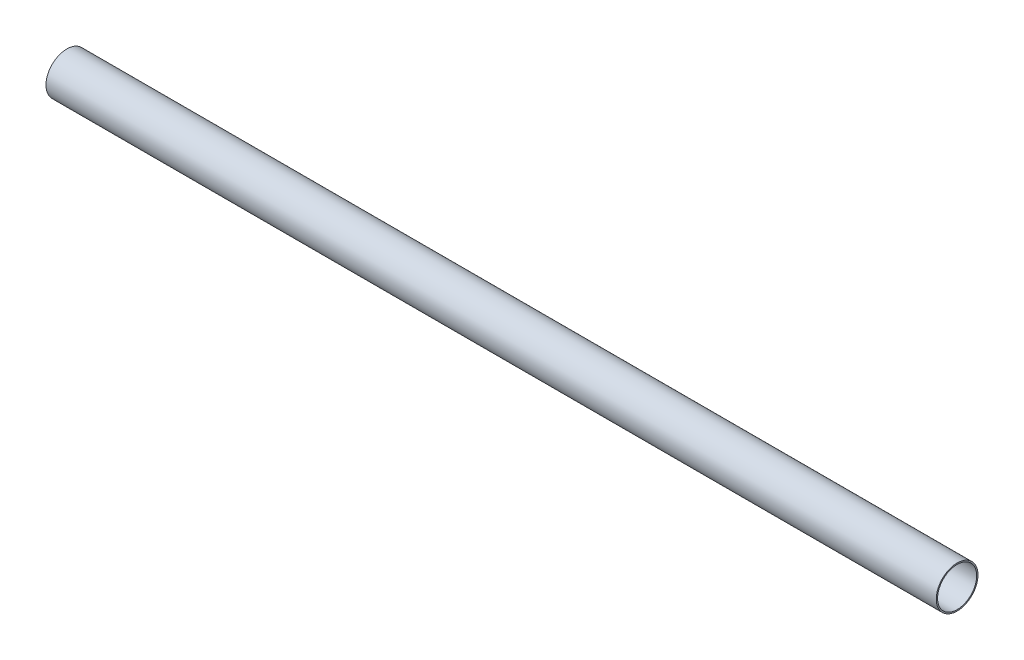
SolidWorks part; units mm, degrees
ref_plane "Front" through (0, 0, 0) normal (0, 0, 1) x (1, 0, 0)
ref_plane "Top" through (0, 0, 0) normal (0, 1, 0) x (1, 0, 0)
ref_plane "Right" through (0, 0, 0) normal (1, 0, 0) x (0, 0, -1)
sketch "Sketch1" plane through (0, 0, 0) normal (1, 0, 0) x (0, 0, -1)
  circle A0 centre (0, 0) radius 14.2875
  circle A1 centre (0, 0) radius 13.3985
  point P4 (14.2875, 0)
  point P5 (13.3985, 0)
  dimension "OD" = 28.575
  dimension "ID" = 26.797
  dimension "Wall" = 0.889
extrude "Extrude1" add sketch "Sketch1" along normal mid plane 609.6
sketch "Sketch2" plane through (0, 0, 0) normal (0, 0, 1) x (1, 0, 0)
  line L0 (-304.8, 0) -> (304.8, 0) construction
  line L1 (-304.8, 14.2875) -> (-304.8, -14.2875) construction
